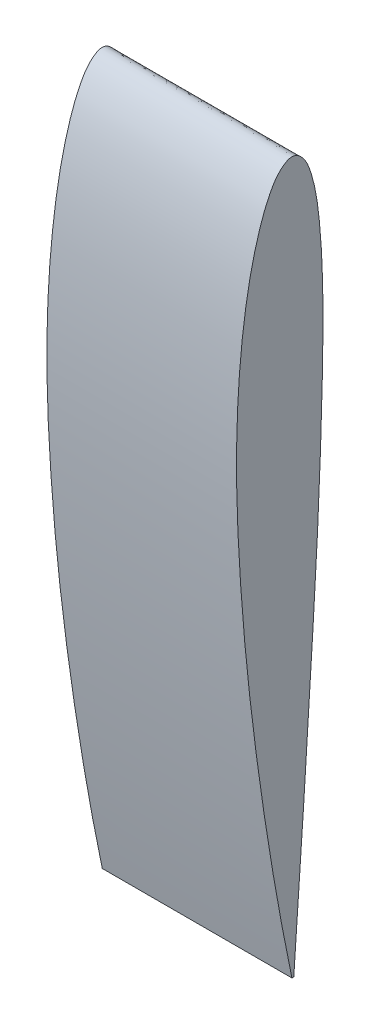
SolidWorks part; units mm, degrees
ref_plane "Front Plane" through (0, 0, 0) normal (0, 0, 1) x (1, 0, 0)
ref_plane "Top Plane" through (0, 0, 0) normal (0, 1, 0) x (1, 0, 0)
ref_plane "Right Plane" through (0, 0, 0) normal (1, 0, 0) x (0, 0, -1)
curve "Curve1"
  spline degree 3 poles (1, 0.0013, 0) (0.9833, 0.0047, 0) (0.9501, 0.0115, 0) (0.8835, 0.024, 0) (0.8002, 0.0379, 0) (0.7002, 0.0522, 0) (0.6002, 0.0641, 0) (0.5001, 0.0729, 0) (0.4001, 0.0788, 0) (0.3166, 0.0798, 0) (0.2499, 0.077, 0) (0.1999, 0.073, 0) (0.1498, 0.0666, 0) (0.108, 0.0587, 0) (0.0748, 0.0498, 0) (0.0496, 0.0416, 0) (0.0282, 0.0322, 0) (0.0098, 0.0207, 0) (-0.0063, 0.0009, 0) (0.0104, -0.0165, 0) (0.0285, -0.0245, 0) (0.0497, -0.0305, 0) (0.0749, -0.0348, 0) (0.1083, -0.0385, 0) (0.1499, -0.0414, 0) (0.2, -0.0425, 0) (0.25, -0.0424, 0) (0.3167, -0.0409, 0) (0.4, -0.0382, 0) (0.5, -0.0336, 0) (0.6, -0.0276, 0) (0.7, -0.0214, 0) (0.8, -0.0151, 0) (0.8833, -0.0093, 0) (0.95, -0.0048, 0) (0.9833, -0.0025, 0) (1, -0.0013, 0) knots 0 0 0 0 0.025012 0.049959 0.099673 0.149206 0.198581 0.247805 0.296917 0.345953 0.370492 0.395091 0.419815 0.444799 0.45749 0.470406 0.483879 0.491264 0.503459 0.513609 0.520451 0.533235 0.545691 0.558032 0.582609 0.607135 0.631652 0.656174 0.705234 0.75432 0.803437 0.852566 0.901701 0.950849 0.975423 1 1 1 1
sketch "Sketch1" plane through (0, 0, 0) normal (0, 0, 1) x (1, 0, 0)
  line L0 (-30.2439, 0) -> (269.7561, 0) construction
  line L1 (269.7561, 0.39) -> (269.7561, -0.39)
  spline S1 degree 3 poles (269.7561, 0.39) (264.7588, 1.414) (254.7775, 3.4593) (234.7977, 7.2056) (209.8095, 11.3564) (179.8038, 15.6525) (149.8031, 19.2352) (119.7893, 21.8586) (89.7824, 23.6351) (64.7467, 23.9358) (44.7379, 23.1075) (29.719, 21.8937) (14.6812, 19.9716) (2.166, 17.6048) (-7.8114, 14.927) (-15.3757, 12.4925) (-21.7845, 9.6559) (-27.3126, 6.2169) (-32.1334, 0.2696) (-27.1259, -4.9579) (-21.7011, -7.3422) (-15.3205, -9.1532) (-7.7812, -10.4518) (2.2361, -11.56) (14.7402, -12.4129) (29.7543, -12.7549) (44.7577, -12.7072) (64.7596, -12.2657) (89.7642, -11.4712) (119.7661, -10.0886) (149.7593, -8.2916) (179.7575, -6.4237) (209.7609, -4.5329) (234.7555, -2.7916) (254.7573, -1.4485) (264.7563, -0.7428) (269.7561, -0.39) knots 0 0 0 0 0.025012 0.049959 0.099673 0.149206 0.198581 0.247805 0.296917 0.345953 0.370492 0.395091 0.419815 0.444799 0.45749 0.470406 0.483879 0.491264 0.503459 0.513609 0.520451 0.533235 0.545691 0.558032 0.582609 0.607135 0.631652 0.656174 0.705234 0.75432 0.803437 0.852566 0.901701 0.950849 0.975423 1 1 1 1
  point P3 (44.7561, 5)
  point P11 (194.7561, 0)
  dimension "D3" = 75
  dimension "D2" = 5
  dimension "D5" = 75
extrude "Boss-Extrude1" add sketch "Sketch1" along normal blind 80
move or copy body "Body-Move/Copy1" bodies to move or copy 101 copy no rotation origin (0, 0, 0) rotation axis (0.5774, -0.5774, -0.5774) rotation angle 120
